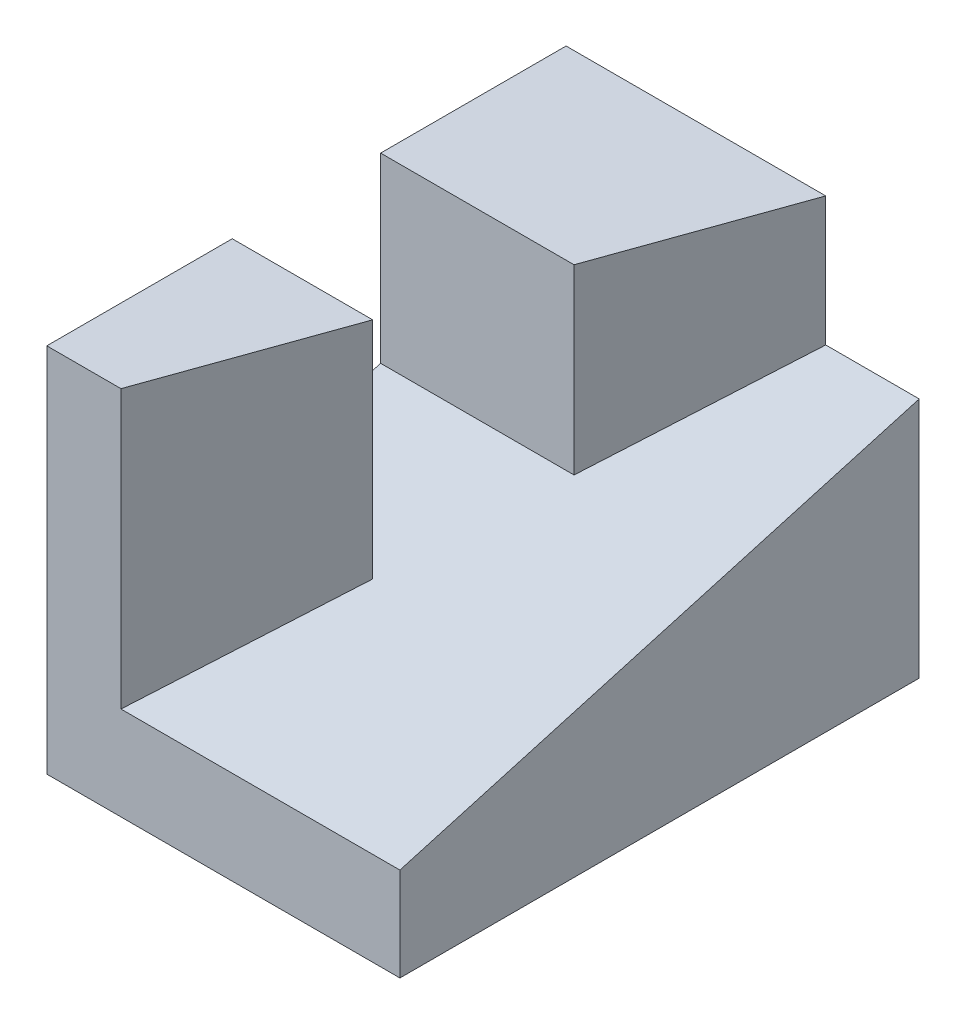
SolidWorks part; units mm, degrees
material "Copper"
ref_plane "Front Plane" through (0, 0, 0) normal (0, 0, 1) x (1, 0, 0)
ref_plane "Top Plane" through (0, 0, 0) normal (0, 1, 0) x (1, 0, 0)
ref_plane "Right Plane" through (0, 0, 0) normal (1, 0, 0) x (0, 0, -1)
sketch "Sketch3" plane through (0, 0, 0) normal (0, 1, 0) x (1, 0, 0)
  line L1 (0, 88.9) -> (60.452, 88.9)
  line L2 (0, 88.9) -> (0, 0)
  line L3 (0, 0) -> (60.452, 0)
  line L4 (60.452, 88.9) -> (60.452, 0)
  dimension "D1" = 60.452
  dimension "D2" = 88.9
extrude "Boss-Extrude1" add sketch "Sketch3" along normal blind 63.5
sketch "Sketch4" plane through (0, 0, 0) normal (1, 0, 0) x (0, 0, -1)
  line L0 (88.9, 41.402) -> (0, 16.002)
  line L4 (0, 0) -> (88.9, 0)
  line L5 (88.9, 0) -> (88.9, 63.5)
  line L6 (88.9, 63.5) -> (0, 63.5)
  line L7 (0, 63.5) -> (0, 0)
  line L8 (0, 0) -> (88.9, 0)
  line L9 (88.9, 0) -> (88.9, 63.5)
  line L10 (88.9, 63.5) -> (0, 63.5)
  line L11 (0, 63.5) -> (0, 0)
  dimension "D2" = 16.002
  dimension "D3" = 41.402
  dimension "D1" = 0
extrude "Cut-Extrude1" cut sketch "Sketch4" along normal blind 63.5 contours L10 L11 L0 L9
sketch "Sketch5" plane through (0, 0, 0) normal (0, 1, 0) x (1, 0, 0)
  line L0 (18.1078, 88.9) -> (0.0134, 88.5864)
  line L1 (44.45, 88.9) -> (12.7, 0)
  line L2 (0, 31.75) -> (24.0393, 31.75)
  line L3 (0, 57.15) -> (33.1107, 57.15)
  line L4 (60.452, 88.9) -> (0, 88.9)
  line L5 (0, 88.9) -> (0, 0)
  line L6 (0, 0) -> (60.452, 0)
  line L7 (60.452, 0) -> (60.452, 88.9)
  line L8 (60.452, 88.9) -> (0, 88.9)
  line L9 (0, 88.9) -> (0, 0)
  line L10 (0, 0) -> (60.452, 0)
  line L11 (60.452, 0) -> (60.452, 88.9)
  point P2 (12.7, 0)
  point P4 (0, 31.75)
  point P6 (0, 57.15)
  point P7 (44.45, 88.9)
  dimension "D2" = 12.7
  dimension "D3" = 31.75
  dimension "D4" = 25.4
  dimension "D5" = 44.45
  dimension "D1" = 0
extrude "Boss-Extrude2" add sketch "Sketch5" along normal blind 63.5
